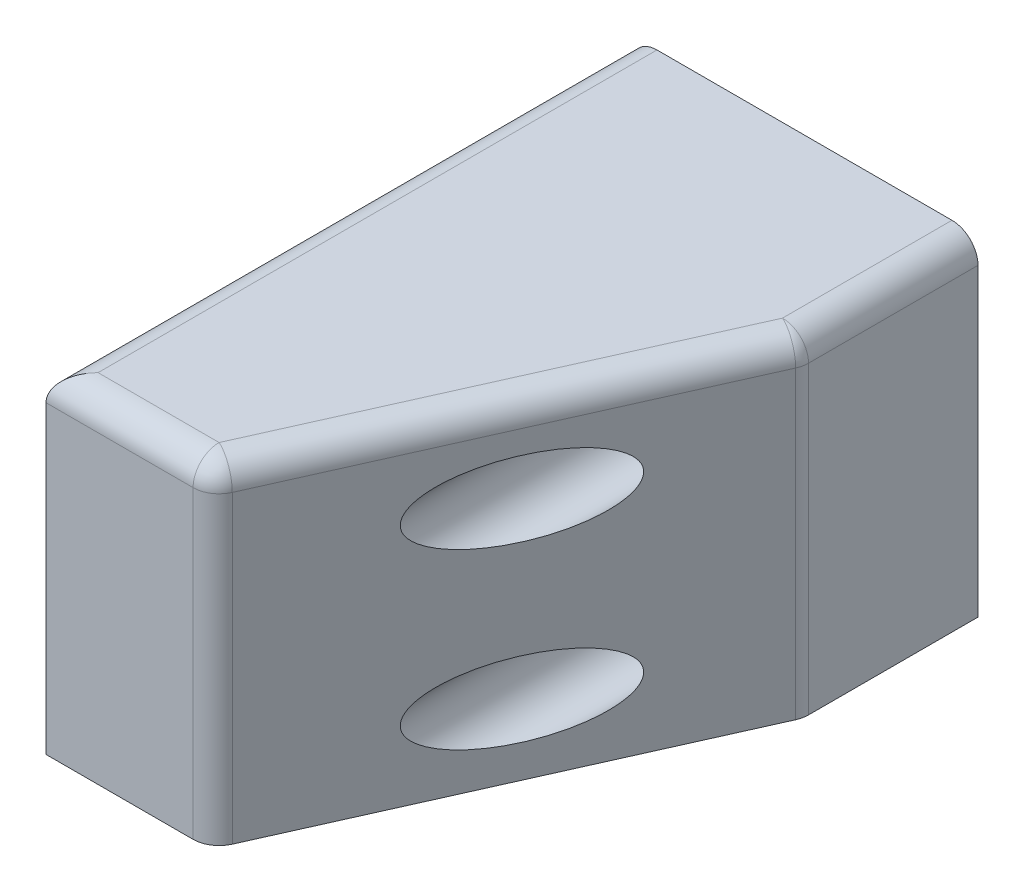
SolidWorks part; units mm, degrees
ref_plane "Front Plane" through (0, 0, 0) normal (1, 0, 0) x (0, 1, 0)
ref_plane "Top Plane" through (0, 0, 0) normal (0, 0, 1) x (0, 1, 0)
ref_plane "Right Plane" through (0, 0, 0) normal (0, 1, 0) x (-1, 0, 0)
sketch "Sketch1" plane through (0, 0, 0) normal (0, 0, 1) x (0, 1, 0)
  line L1 (0, 0) -> (48.4, 0)
  line L2 (0, 0) -> (0, 50.8)
  line L3 (0, 50.8) -> (48.4, 50.8)
  line L4 (48.4, 0) -> (48.4, 50.8)
  dimension "D1" = 48.4
  dimension "D2" = 50.8
extrude "Boss-Extrude1" add sketch "Sketch1" along normal blind 85.62
sketch "Sketch2" plane through (0, 48.4, 0) normal (0, 1, 0) x (-1, 0, 0)
  line L0 (26.8, 85.62) -> (0, 25.62)
  line L1 (0, 85.62) -> (50.8, 85.62) construction
  line L2 (0, 85.62) -> (0, 0) construction
  line L3 (26.8, 85.62) -> (0, 85.62)
  line L4 (0, 85.62) -> (0, 25.62)
  line L5 (50.8, 85.62) -> (50.8, 0) construction
  dimension "D1" = 24
  dimension "D2" = 60
extrude "Cut-Extrude1" cut sketch "Sketch2" against normal through all
sketch "Sketch3" plane through (0, 0, 0) normal (0, 0, -1) x (1, 0, 0)
  line L0 (-43.8, 0) -> (-43.8, -3)
  line L1 (-50.8, 0) -> (0, 0) construction
  line L2 (-43.8, -3) -> (-46.8, -3)
  line L3 (-46.8, -3) -> (-46.8, -15)
  line L4 (-46.8, -15) -> (-30.8, -15)
  line L5 (-30.8, -15) -> (-30.8, -3)
  line L6 (-30.8, -3) -> (-33.8, -3)
  line L7 (-33.8, -3) -> (-33.8, 0)
  line L8 (-43.8, 0) -> (-33.8, 0)
  line L9 (-50.8, -48.4) -> (-50.8, 0) construction
  dimension "D1" = 10
  dimension "D2" = 3
  dimension "D3" = 16
  dimension "D4" = 12
  dimension "D5" = 4
extrude "Cut-Extrude2" cut sketch "Sketch3" against normal blind 70
sketch "Sketch4" plane through (-50.8, 0, 0) normal (-1, 0, 0) x (0, -1, 0)
  line L1 (-48.4, 0) -> (-38, 0) construction
  line L2 (-48.4, 0) -> (-48.4, 35.6) construction
  line L3 (-48.4, 35.6) -> (-38, 35.6) construction
  line L4 (-38, 0) -> (-38, 35.6) construction
  circle A0 centre (-38, 35.6) radius 3.25
  dimension "D3" = 6.5
  dimension "D1" = 10.4
  dimension "D2" = 35.6
sketch "Sketch5" plane through (0, 0, 85.62) normal (0, 0, 1) x (1, 0, 0)
  line L0 (-12.7, 35.7) -> (-12.7, 10.3) construction
  line L1 (0, 48.4) -> (-12.7, 48.4) construction
  line L2 (0, 48.4) -> (0, 35.7) construction
  line L3 (0, 35.7) -> (-12.7, 35.7) construction
  line L4 (-12.7, 48.4) -> (-12.7, 35.7) construction
  circle A0 centre (-12.7, 10.3) radius 5.5
  circle A1 centre (-12.7, 35.7) radius 5.5
  dimension "D3" = 11
  dimension "D1" = 12.7
  dimension "D2" = 25.4
extrude "Cut-Extrude3" cut sketch "Sketch5" against normal blind 80
sketch "Sketch6" plane through (0, 0, 5.62) normal (0, 0, 1) x (1, 0, 0)
  circle A0 centre (-12.7, 35.7) radius 3.25
  circle A1 centre (-12.7, 10.3) radius 3.25
  dimension "D1" = 6.5
extrude "Cut-Extrude4" cut sketch "Sketch6" against normal through all
ref_plane "Plane1" through (-38.8, 0, 0) normal (-1, 0, 0) x (0, 0, 1)
sketch "Sketch7" plane through (-38.8, 0, 0) normal (-1, 0, 0) x (0, 0, 1)
  line L1 (35.6, 43.7735) -> (30.6, 40.8868)
  line L2 (30.6, 40.8868) -> (30.6, 35.1132)
  line L3 (30.6, 35.1132) -> (35.6, 32.2265)
  line L4 (35.6, 32.2265) -> (40.6, 35.1132)
  line L5 (40.6, 35.1132) -> (40.6, 40.8868)
  line L6 (40.6, 40.8868) -> (35.6, 43.7735)
  circle A0 centre (35.6, 38) radius 5 construction
  dimension "D1" = 10
extrude "Cut-Extrude5" cut sketch "Sketch7" against normal blind 3 and the other way blind 3
sketch "Sketch8" plane through (0, 15, 0) normal (0, -1, 0) x (1, 0, 0)
  line L0 (-41.8, 40.6) -> (-35.8, 40.6)
  line L3 (-41.8, 30.6) -> (-35.8, 30.6)
  line L6 (-41.8, 40.6) -> (-41.8, 30.6)
  line L7 (-35.8, 40.6) -> (-35.8, 30.6)
  point P0 (0, 0)
  point P3 (-38.8, 40.6)
  point P6 (-38.8, 30.6)
  dimension "D1" = 6
extrude "Cut-Extrude6" cut sketch "Sketch8" against normal up to next
extrude "Cut-Extrude7" cut sketch "Sketch4" against normal up to next
fillet "Fillet1" radius 3.81 6 edges at (-26.8, 24.2, 85.62) (0, 24.2, 25.62) (0, 48.4, 12.81) (-13.4, 48.4, 55.62) (-50.8, 48.4, 42.81) (-38.8, 48.4, 85.62)
